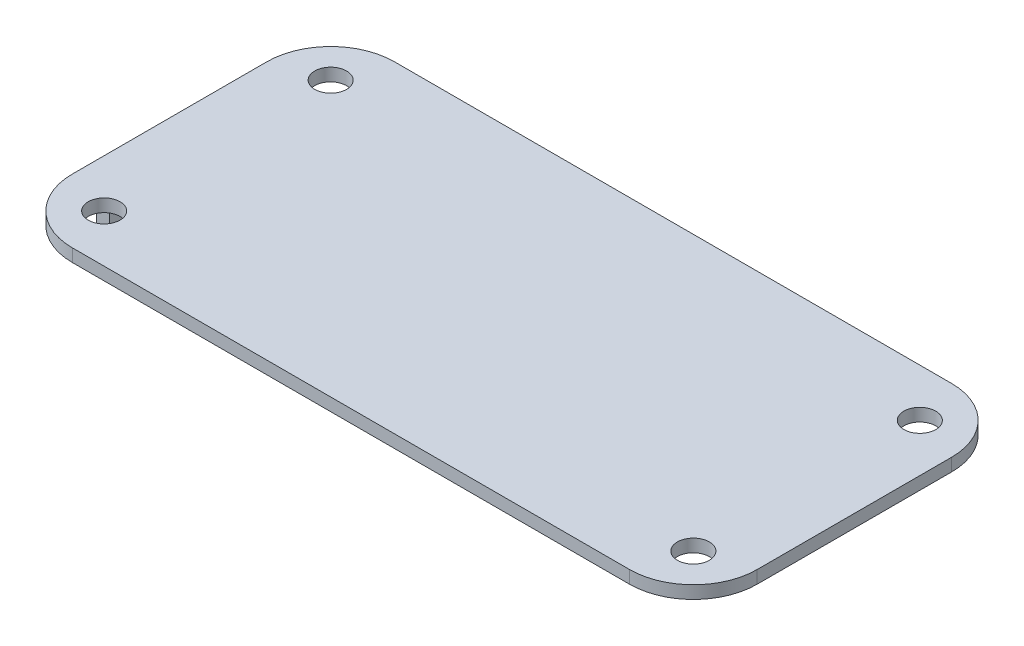
SolidWorks part; units mm, degrees
ref_plane "Front Plane" through (0, 0, 0) normal (0, 0, 1) x (1, 0, 0)
ref_plane "Top Plane" through (0, 0, 0) normal (0, 1, 0) x (1, 0, 0)
ref_plane "Right Plane" through (0, 0, 0) normal (1, 0, 0) x (0, 0, -1)
sketch "Sketch1" plane through (0, 0, 0) normal (0, 1, 0) x (1, 0, 0)
  line L1 (-87.35, -50.5) -> (87.35, -50.5)
  line L2 (-107.35, -30.5) -> (-107.35, 30.5)
  line L3 (-87.35, 50.5) -> (87.35, 50.5)
  line L4 (107.35, -30.5) -> (107.35, 30.5)
  line L5 (-107.35, -50.5) -> (107.35, 50.5) construction
  line L6 (-107.35, 50.5) -> (107.35, -50.5) construction
  arc A0 (87.35, -50.5) -> (107.35, -30.5) centre (87.35, -30.5) ccw
  arc A1 (87.35, 50.5) -> (107.35, 30.5) centre (87.35, 30.5) cw
  arc A2 (-87.35, -50.5) -> (-107.35, -30.5) centre (-87.35, -30.5) cw
  arc A3 (-107.35, 30.5) -> (-87.35, 50.5) centre (-87.35, 30.5) cw
  circle A4 centre (-92.35, 35.5) radius 5
  circle A5 centre (92.35, 35.5) radius 5
  circle A6 centre (92.35, -35.5) radius 5
  circle A7 centre (-92.35, -35.5) radius 5
  point P0 (0, 0)
  dimension "D3" = 20
  dimension "D4" = 10
  dimension "D1" = 101
  dimension "D2" = 214.7
  dimension "D5" = 15
  dimension "D6" = 15
  dimension "D9" = 15
  dimension "D10" = 15
  dimension "D7" = 2
  dimension "D8" = 2
extrude "Boss-Extrude1" add sketch "Sketch1" along normal blind 4
sketch "Sketch2" plane through (0, 4, 0) normal (0, 1, 0) x (1, 0, 0)
  line L0 (87.35, 50.5) -> (-87.35, 50.5) construction
  line L1 (-87.35, 16.85) -> (-49.35, 16.85)
  line L2 (-87.35, 16.85) -> (-87.35, -16.85)
  line L3 (-87.35, -16.85) -> (-49.35, -16.85)
  line L4 (-49.35, 16.85) -> (-49.35, -16.85)
  line L5 (-87.35, 16.85) -> (-49.35, -16.85) construction
  line L6 (-87.35, -16.85) -> (-49.35, 16.85) construction
  line L7 (-107.35, 30.5) -> (-107.35, -30.5) construction
  line L8 (-87.35, -50.5) -> (87.35, -50.5) construction
  line L9 (-43.4096, 39.8) -> (8.9804, 39.8)
  line L10 (-43.4096, 39.8) -> (-43.4096, -39.8)
  line L11 (-43.4096, -39.8) -> (8.9804, -39.8)
  line L12 (8.9804, 39.8) -> (8.9804, -39.8)
  line L13 (-43.4096, 39.8) -> (8.9804, -39.8) construction
  line L14 (-43.4096, -39.8) -> (8.9804, 39.8) construction
  line L15 (46.45, 30.28) -> (103.35, 30.28)
  line L16 (46.45, 30.28) -> (46.45, -30.28)
  line L17 (46.45, -30.28) -> (103.35, -30.28)
  line L18 (103.35, 30.28) -> (103.35, -30.28)
  line L19 (46.45, 30.28) -> (103.35, -30.28) construction
  line L20 (46.45, -30.28) -> (103.35, 30.28) construction
  line L21 (107.35, -30.5) -> (107.35, 30.5) construction
  line L22 (18.6612, 22) -> (39.6612, 22)
  line L23 (18.6612, 22) -> (18.6612, -22)
  line L24 (18.6612, -22) -> (39.6612, -22)
  line L25 (39.6612, 22) -> (39.6612, -22)
  line L26 (18.6612, 22) -> (39.6612, -22) construction
  line L27 (18.6612, -22) -> (39.6612, 22) construction
  line L29 (-107.35, 22.85) -> (-103.35, 22.85)
  line L30 (-107.35, 22.85) -> (-107.35, -22.85)
  line L31 (-107.35, -22.85) -> (-103.35, -22.85)
  line L32 (-103.35, 22.85) -> (-103.35, -22.85)
  point P0 (-68.35, 0)
  point P10 (-17.2146, 0)
  point P15 (74.9, 0)
  point P22 (29.1612, 0)
  point P32 (-105.35, -22.85)
  line M11 (-107.35, 30.5) -> (-107.35, -30.5)
  dimension "D1" = 33.7
  dimension "D2" = 38
  dimension "D3" = 33.65
  dimension "D4" = 20
  dimension "D5" = 79.6
  dimension "D6" = 52.39
  dimension "D7" = 10.7
  dimension "D8" = 60.56
  dimension "D9" = 56.9
  dimension "D10" = 20.22
  dimension "D11" = 44
  dimension "D12" = 21
  dimension "D13" = 28.5
  dimension "D14" = 4
  dimension "D15" = 45.7
  dimension "D16" = 4
  dimension "D17" = 27.65
extrude "Boss-Extrude2" add sketch "Sketch2" against normal blind 21.3 contours L32 L29 L31 M11
equation "\"D3@Sketch2\"=(\"D1@Sketch1\"-\"D1@Sketch2\")/2"
equation "\"D7@Sketch2\"=(\"D1@Sketch1\"-\"D5@Sketch2\")/2"
equation "\"D10@Sketch2\"=(\"D1@Sketch1\"-\"D8@Sketch2\")/2"
equation "\"D9@Sketch1\"=\"D5@Sketch1\""
equation "\"D10@Sketch1\"=\"D6@Sketch1\""
equation "\"D13@Sketch2\"=(\"D1@Sketch1\"-\"D11@Sketch2\")/2"
equation "\"D17@Sketch2\"=(\"D1@Sketch1\"-\"D15@Sketch2\")/2"
